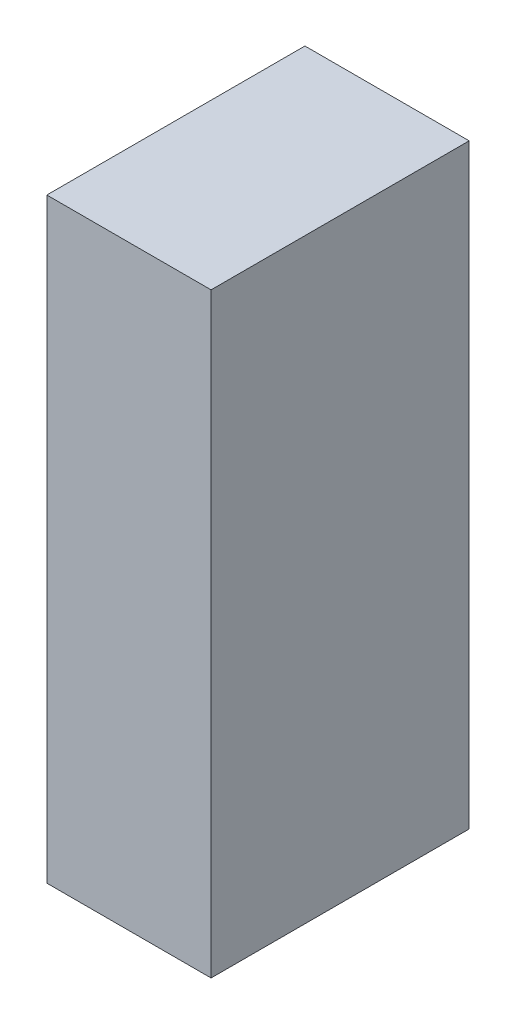
SolidWorks part; units mm, degrees
ref_plane "Front Plane" through (0, 0, 0) normal (0, 0, 1) x (1, 0, 0)
ref_plane "Top Plane" through (0, 0, 0) normal (0, 1, 0) x (1, 0, 0)
ref_plane "Right Plane" through (0, 0, 0) normal (1, 0, 0) x (0, 0, -1)
sketch "Sketch1" plane through (0, 0, 0) normal (0, 1, 0) x (1, 0, 0)
  line L1 (-17.5, -27.5) -> (17.5, -27.5)
  line L2 (-17.5, -27.5) -> (-17.5, 27.5)
  line L3 (-17.5, 27.5) -> (17.5, 27.5)
  line L4 (17.5, -27.5) -> (17.5, 27.5)
  line L5 (-17.5, -27.5) -> (17.5, 27.5) construction
  line L6 (-17.5, 27.5) -> (17.5, -27.5) construction
  point P0 (0, 0)
  dimension "D1" = 55
  dimension "D2" = 35
extrude "Boss-Extrude1" add sketch "Sketch1" along normal blind 127
